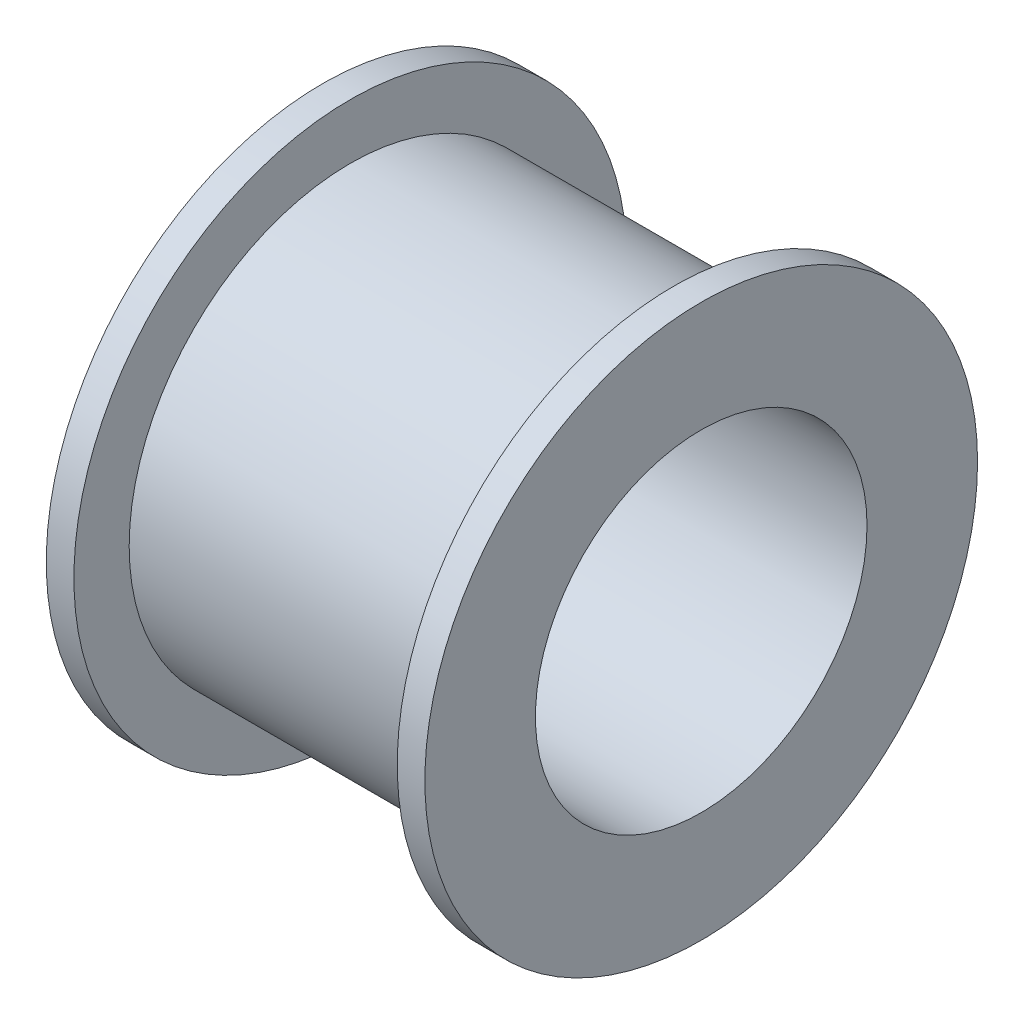
SolidWorks part; units mm, degrees
ref_plane "Front Plane" through (0, 0, 0) normal (0, 0, 1) x (1, 0, 0)
ref_plane "Top Plane" through (0, 0, 0) normal (0, 1, 0) x (1, 0, 0)
ref_plane "Right Plane" through (0, 0, 0) normal (1, 0, 0) x (0, 0, -1)
sketch "Sketch1" plane through (0, 0, 0) normal (0, 0, 1) x (1, 0, 0)
  line L0 (0, 100) -> (0, 60)
  line L1 (0, 100) -> (10, 100)
  line L2 (10, 100) -> (10, 80)
  line L3 (10, 80) -> (68.5, 80)
  line L4 (68.5, 80) -> (68.5, 60)
  line L5 (68.5, 60) -> (0, 60)
  point P0 (0, 0)
  dimension "D1" = 100
  dimension "D2" = 10
  dimension "D3" = 68.5
  dimension "D4" = 80
  dimension "D5" = 60
ref_axis "Axis1" through (71.925, 0, 0) along (-1, 0, 0)
revolve "Revolve1" add sketch "Sketch1" angle 360 about axis through (71.925, 0, 0) along (-1, 0, 0)
mirror "Mirror1" about plane through (68.5, 80, 0) normal (1, 0, 0) of "Revolve1"
